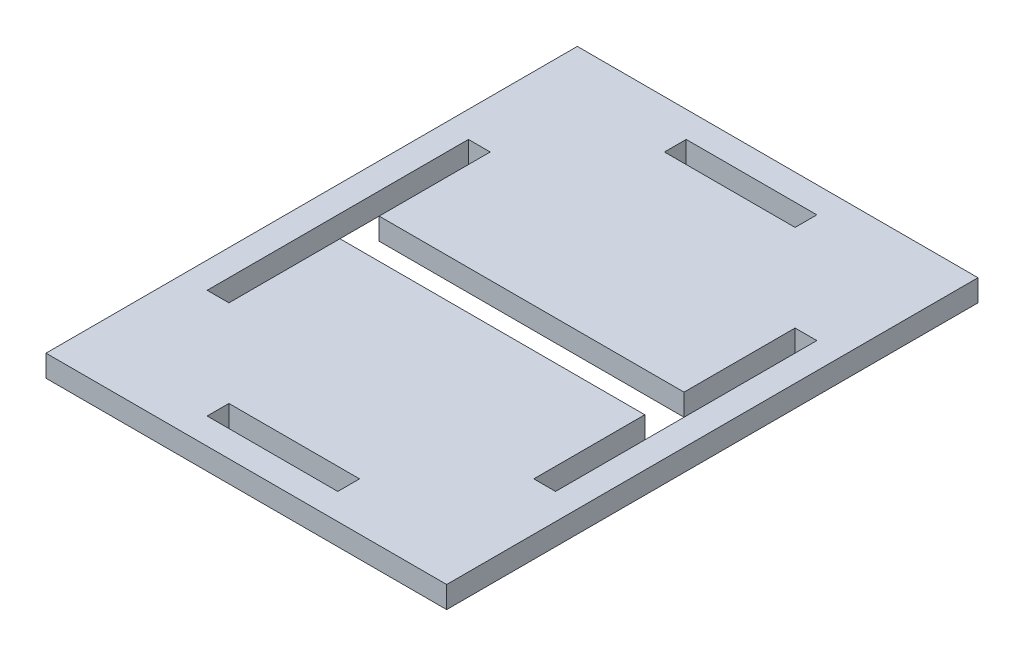
SolidWorks part; units mm, degrees
ref_plane "Front Plane" through (0, 0, 0) normal (0, 0, 1) x (1, 0, 0)
ref_plane "Top Plane" through (0, 0, 0) normal (0, 1, 0) x (1, 0, 0)
ref_plane "Right Plane" through (0, 0, 0) normal (1, 0, 0) x (0, 0, -1)
sketch "Sketch1" plane through (0, 0, 0) normal (0, 1, 0) x (1, 0, 0)
  line L1 (-46, 61) -> (46, 61)
  line L2 (-46, 61) -> (-46, -61)
  line L3 (-46, -61) -> (46, -61)
  line L4 (46, 61) -> (46, -61)
  line L5 (-46, 61) -> (46, -61) construction
  line L6 (-46, -61) -> (46, 61) construction
  point P0 (0, 0)
  dimension "D1" = 92
  dimension "D2" = 122
extrude "Boss-Extrude1" add sketch "Sketch1" along normal blind 5
sketch "Sketch2" plane through (0, 5, 0) normal (0, 1, 0) x (1, 0, 0)
  line L0 (-46, -61) -> (46, -61) construction
  line L1 (-46, 61) -> (-40, 61) construction
  line L2 (-46, 61) -> (-46, -61) construction
  line L3 (-46, -61) -> (-40, -61) construction
  line L4 (-40, 61) -> (-40, -61) construction
  line L6 (46, 61) -> (40, 61) construction
  line L7 (46, 61) -> (46, -61) construction
  line L8 (46, -61) -> (40, -61) construction
  line L9 (40, 61) -> (40, -61) construction
  line L10 (-35, 30) -> (-40, 30)
  line L11 (-35, 30) -> (-35, -30)
  line L12 (-35, -30) -> (-40, -30)
  line L13 (-40, 30) -> (-40, -30)
  line L14 (-35, 30) -> (-40, -30) construction
  line L15 (-35, -30) -> (-40, 30) construction
  line L16 (35, 30) -> (40, 30)
  line L17 (35, 30) -> (35, -30)
  line L18 (35, -30) -> (40, -30)
  line L19 (40, 30) -> (40, -30)
  line L20 (35, 30) -> (40, -30) construction
  line L21 (35, -30) -> (40, 30) construction
  line L22 (-46, 61) -> (46, 61) construction
  line L23 (-46, 61) -> (-46, 55) construction
  line L24 (-46, 55) -> (46, 55) construction
  line L25 (46, 61) -> (46, 55) construction
  line L26 (-46, -61) -> (46, -61) construction
  line L27 (-46, -61) -> (-46, -55) construction
  line L28 (-46, -55) -> (46, -55) construction
  line L29 (46, -61) -> (46, -55) construction
  line L30 (-15, 50) -> (15, 50)
  line L31 (-15, 50) -> (-15, 55)
  line L32 (-15, 55) -> (15, 55)
  line L33 (15, 50) -> (15, 55)
  line L34 (-15, 50) -> (15, 55) construction
  line L35 (-15, 55) -> (15, 50) construction
  line L36 (-15, -50) -> (15, -50)
  line L37 (-15, -50) -> (-15, -55)
  line L38 (-15, -55) -> (15, -55)
  line L39 (15, -50) -> (15, -55)
  line L40 (-15, -50) -> (15, -55) construction
  line L41 (-15, -55) -> (15, -50) construction
  point P12 (-37.5, 0)
  point P17 (37.5, 0)
  point P27 (0, 52.5)
  point P32 (0, -52.5)
  dimension "D1" = 6
  dimension "D2" = 6
  dimension "D3" = 5
  dimension "D4" = 60
  dimension "D5" = 0
  dimension "D6" = 5
  dimension "D7" = 6
  dimension "D8" = 6
  dimension "D9" = 30
  dimension "D10" = 0
  dimension "D11" = 5
  dimension "D12" = 5
extrude "Cut-Extrude1" cut sketch "Sketch2" against normal through all
sketch "Sketch3" plane through (0, 5, 0) normal (0, 1, 0) x (1, 0, 0)
  line L0 (0, 0) -> (-20, 0) construction
  line L1 (-30, 22.5) -> (30, 22.5) construction
  line L2 (-30, 22.5) -> (-30, -22.5) construction
  line L3 (-30, -22.5) -> (30, -22.5) construction
  line L4 (30, 22.5) -> (30, -22.5) construction
  line L5 (-30, 22.5) -> (30, -22.5) construction
  line L6 (-30, -22.5) -> (30, 22.5) construction
  line L7 (0, 0) -> (20, 0) construction
  circle A0 centre (0, 0) radius 4.03
  circle A1 centre (-20, 0) radius 4.03
  circle A2 centre (20, 0) radius 4.03
  point P0 (0, 0)
  dimension "D3" = 20
  dimension "D4" = 20
  dimension "D1" = 60
  dimension "D2" = 45
extrude "Cut-Extrude2" cut sketch "Sketch3" against normal blind 5
sketch "Sketch4" plane through (0, 5, 0) normal (0, 1, 0) x (1, 0, 0)
  line L1 (-35, 4.5) -> (35, 4.5)
  line L2 (-35, 4.5) -> (-35, -4.5)
  line L3 (-35, -4.5) -> (35, -4.5)
  line L4 (35, 4.5) -> (35, -4.5)
  line L5 (-35, 4.5) -> (35, -4.5) construction
  line L6 (-35, -4.5) -> (35, 4.5) construction
  point P0 (0, 0)
  dimension "D1" = 9
  dimension "D2" = 70
extrude "Cut-Extrude3" cut sketch "Sketch4" against normal blind 10
